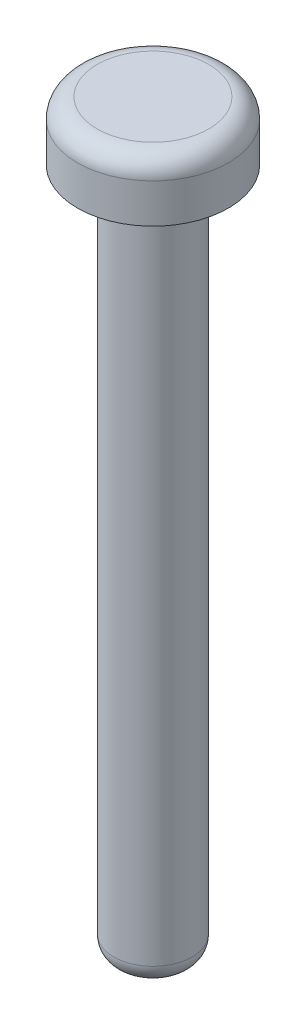
SolidWorks part; units mm, degrees
ref_plane "Спереди" through (0, 0, 0) normal (0, 0, 1) x (1, 0, 0)
ref_plane "Сверху" through (0, 0, 0) normal (0, 1, 0) x (1, 0, 0)
ref_plane "Справа" through (0, 0, 0) normal (1, 0, 0) x (0, 0, -1)
sketch "Sketch1" plane through (0, 0, 0) normal (0, 1, 0) x (1, 0, 0)
  circle A0 centre (0, 0) radius 2
  dimension "D1" = 4
extrude "Boss-Extrude1" add sketch "Sketch1" along normal blind 35
sketch "Sketch2" plane through (0, 35, 0) normal (0, 1, 0) x (1, 0, 0)
  circle A0 centre (0, 0) radius 3.85
  dimension "D1" = 7.7
extrude "Boss-Extrude2" add sketch "Sketch2" along normal blind 3
fillet "Fillet1" radius 1 1 edges at (0, 38, 3.85)
fillet "Fillet2" radius 1 2 edges at (0, 0, 2) (0, 35, 2)
